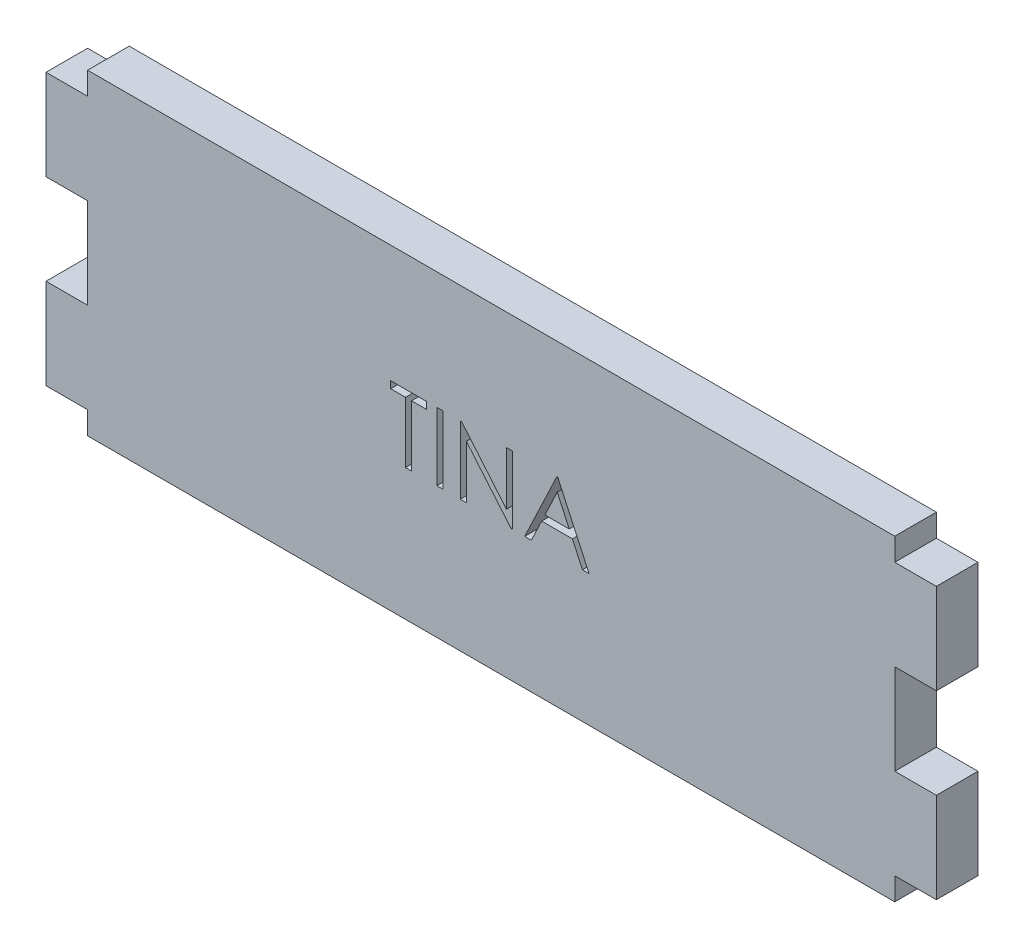
SolidWorks part; units mm, degrees
ref_plane "Front Plane" through (0, 0, 0) normal (0, 0, 1) x (1, 0, 0)
ref_plane "Top Plane" through (0, 0, 0) normal (0, 1, 0) x (1, 0, 0)
ref_plane "Right Plane" through (0, 0, 0) normal (1, 0, 0) x (0, 0, -1)
sketch "Sketch1" plane through (0, 0, 0) normal (0, 0, 1) x (1, 0, 0)
  line L0 (-56.642, 0) -> (56.642, 0) construction
  line L1 (56.642, -22.225) -> (-56.642, -22.225)
  line L2 (56.642, -22.225) -> (56.642, -19.05)
  line L3 (56.642, 22.225) -> (-56.642, 22.225)
  line L4 (-56.642, -22.225) -> (-56.642, -19.05)
  line L5 (56.642, -22.225) -> (-56.642, 22.225) construction
  line L6 (56.642, 22.225) -> (-56.642, -22.225) construction
  line L7 (-62.484, -19.05) -> (-56.642, -6.35) construction
  line L8 (-62.484, 6.35) -> (-56.642, 6.35)
  line L9 (-62.484, 6.35) -> (-62.484, 19.05)
  line L10 (-62.484, 19.05) -> (-56.642, 19.05)
  line L11 (-56.642, -6.35) -> (-56.642, 6.35)
  line L12 (-62.484, 6.35) -> (-56.642, 19.05) construction
  line L13 (-62.484, 19.05) -> (-56.642, 6.35) construction
  line L14 (-62.484, -6.35) -> (-56.642, -19.05) construction
  line L15 (56.642, -6.35) -> (56.642, 6.35)
  line L16 (-62.484, -19.05) -> (-56.642, -19.05)
  line L17 (-62.484, -6.35) -> (-62.484, -19.05)
  line L18 (-62.484, -6.35) -> (-56.642, -6.35)
  line L19 (0, 22.225) -> (0, -22.225) construction
  line L20 (62.484, -6.35) -> (56.642, -19.05) construction
  line L21 (62.484, 19.05) -> (56.642, 6.35) construction
  line L22 (62.484, 6.35) -> (56.642, 19.05) construction
  line L23 (62.484, -19.05) -> (56.642, -6.35) construction
  line L24 (62.484, -6.35) -> (56.642, -6.35)
  line L25 (62.484, -6.35) -> (62.484, -19.05)
  line L26 (62.484, -19.05) -> (56.642, -19.05)
  line L27 (56.642, 19.05) -> (56.642, 22.225)
  line L28 (56.642, 19.05) -> (56.642, 22.225)
  line L29 (62.484, 19.05) -> (56.642, 19.05)
  line L30 (62.484, 6.35) -> (62.484, 19.05)
  line L31 (62.484, 6.35) -> (56.642, 6.35)
  line L32 (56.642, -22.225) -> (56.642, -19.05)
  line L33 (-56.642, 19.05) -> (-56.642, 22.225)
  line L34 (56.642, -6.35) -> (56.642, 6.35)
  point P0 (0, 0)
  point P8 (-59.563, 12.7)
  point P17 (-59.563, -12.7)
  point P28 (59.563, -12.7)
  point P29 (59.563, 12.7)
  dimension "D1" = 113.284
  dimension "D2" = 44.45
  dimension "D3" = 5.842
  dimension "D4" = 12.7
  dimension "D5" = 12.7
extrude "Boss-Extrude1" add sketch "Sketch1" along normal blind 5.842 contours L33 L10 L9 L8 L11 L18 L17 L16 L4 L1 L2 L32 L15 L27 L3
sketch "Sketch2" plane through (0, 0, 5.842) normal (0, 0, 1) x (1, 0, 0)
  line L0 (-56.642, -3.7757) -> (56.642, -3.7757) construction
  line L1 (-56.642, -6.35) -> (-56.642, 6.35) construction
  line L2 (56.642, -6.35) -> (56.642, 6.35) construction
  text T0 "TINA" font "Century Gothic" height in points 36
extrude "Cut-Extrude1" cut sketch "Sketch2" against normal blind 3.175
